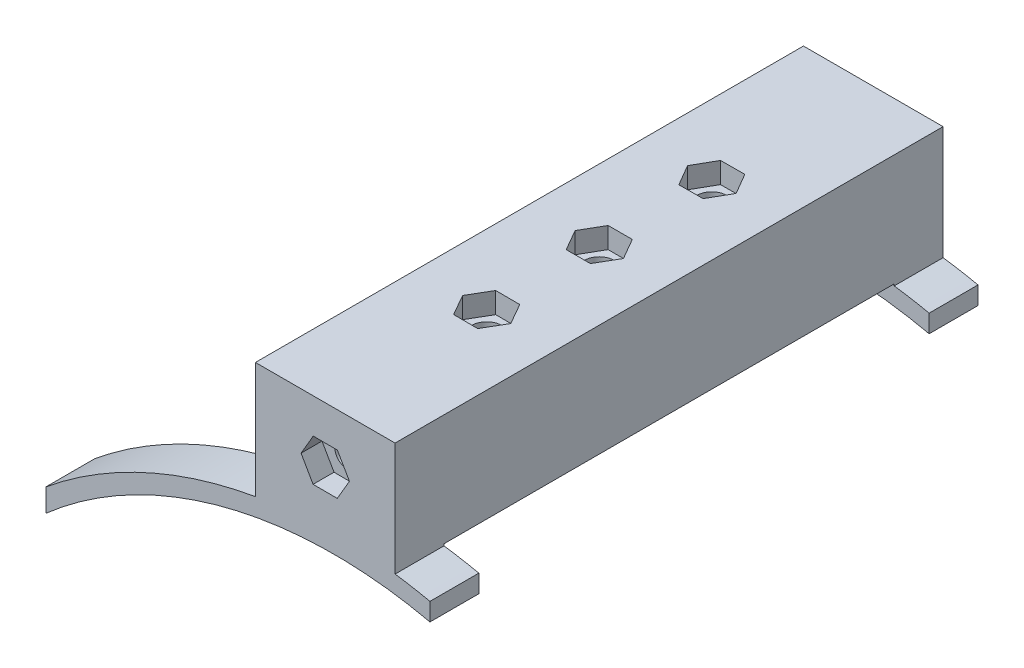
SolidWorks part; units mm, degrees
ref_plane "Front Plane" through (0, 0, 0) normal (0, 0, 1) x (1, 0, 0)
ref_plane "Top Plane" through (0, 0, 0) normal (0, 1, 0) x (1, 0, 0)
ref_plane "Right Plane" through (0, 0, 0) normal (1, 0, 0) x (0, 0, -1)
sketch "Sketch1" plane through (0, 0, 0) normal (0, 0, 1) x (1, 0, 0)
  line L2 (0.4722, 8.3889) -> (0.4722, 5.3889)
  line L3 (0.4722, -7.6111) -> (0.4722, -4.6111)
  line L4 (0.4722, -4.6111) -> (0.4722, 5.3889)
  line L9 (0.4722, 8.3889) -> (-17.5278, 8.3889)
  line L10 (0.4722, 8.3889) -> (0.4722, 5.3889)
  line L12 (0.4722, -7.6111) -> (-17.5278, -7.6111)
  line L13 (-17.5278, 8.3889) -> (-17.5278, -7.6111)
  line L14 (0.4722, 8.3889) -> (-17.5278, -7.6111) construction
  line L15 (0.4722, -7.6111) -> (-17.5278, 8.3889) construction
  line L17 (0.4722, -4.6111) -> (0.4722, -7.6111)
  point P14 (-8.5278, 0.3889)
  dimension "D2" = 18
extrude "Boss-Extrude2" add sketch "Sketch1" along normal blind 48.5
sketch "Sketch2" plane through (-17.5278, 0, 0) normal (-1, 0, 0) x (0, 0, 1)
  line L0 (48.5, 8.3889) -> (62.5, 8.3889)
  line L1 (63.5, 7.3889) -> (63.5, -6.6111)
  line L2 (62.5, -7.6111) -> (48.5, -7.6111)
  line L3 (58.5, -4.6111) -> (58.5, 5.3889) construction
  line L4 (62.5, 8.3889) -> (63.5, 8.3889)
  line L5 (63.5, 8.3889) -> (63.5, 7.3889)
  line L8 (48.5, 8.3889) -> (48.5, -7.6111) construction
  line L12 (48.5, 8.3889) -> (48.5, 5.5889)
  line L13 (48.5, -4.8111) -> (48.5, -7.6111)
  line L14 (24.25, 8.3889) -> (24.25, 19.6589) construction
  line L15 (48.5, 8.3889) -> (0, 8.3889) construction
  line L16 (0, -4.8111) -> (0, -7.6111)
  line L17 (0, 8.3889) -> (0, 5.5889)
  line L21 (-14, -7.6111) -> (0, -7.6111)
  line L22 (-15, 7.3889) -> (-15, -6.6111)
  line L23 (0, 8.3889) -> (-14, 8.3889)
  line L24 (63.5, -6.6111) -> (63.5, -7.6111)
  line L25 (63.5, -7.6111) -> (62.5, -7.6111)
  line L26 (-15, 7.3889) -> (-15, 8.3889)
  line L27 (-15, 8.3889) -> (-14, 8.3889)
  line L28 (-15, -6.6111) -> (-15, -7.6111)
  line L29 (-15, -7.6111) -> (-14, -7.6111)
  line L30 (48.5, 5.5889) -> (48.5, -4.8111)
  line L31 (0, 5.5889) -> (0, -4.8111)
  dimension "D1" = 5
extrude "Boss-Extrude3" add sketch "Sketch2" against normal blind 18
sketch "Sketch3" plane through (0, 0, 63.5) normal (0, 0, 1) x (1, 0, 0)
  circle A0 centre (-9.5278, 0.3889) radius 1.6
  dimension "D1" = 3.2
extrude "Cut-Extrude1" cut sketch "Sketch3" against normal blind 8
ref_plane "Plane1" through (0, 0, 24.25) normal (0, 0, 1) x (1, 0, 0)
mirror "Mirror1" about plane through (0, 0, 24.25) normal (0, 0, 1) of "Cut-Extrude1"
sketch "Sketch4" plane through (0, 0, 63.5) normal (0, 0, 1) x (1, 0, 0)
  line L1 (-7.808, -2.6181) -> (-6.0638, 0.3749)
  line L2 (-6.0638, 0.3749) -> (-7.7837, 3.3819)
  line L3 (-7.7837, 3.3819) -> (-11.2477, 3.3959)
  line L4 (-11.2477, 3.3959) -> (-12.9919, 0.4029)
  line L5 (-12.9919, 0.4029) -> (-11.272, -2.604)
  line L6 (-11.272, -2.604) -> (-7.808, -2.6181)
  circle A0 centre (-9.5278, 0.3889) radius 3 construction
  dimension "D1" = 6
extrude "Cut-Extrude3" cut sketch "Sketch4" against normal blind 3
mirror "Mirror2" about plane through (0, 0, 24.25) normal (0, 0, 1) of "Cut-Extrude3"
sketch "Sketch5" plane through (-17.5278, 0, 0) normal (-1, 0, 0) x (0, 0, 1)
  line L4 (-15, -7.6111) -> (63.5, -7.6111)
  line L5 (63.5, -7.6111) -> (63.5, 8.3889)
  line L6 (63.5, 8.3889) -> (-15, 8.3889)
  line L7 (-15, 8.3889) -> (-15, -7.6111)
  line L8 (-15, -7.6111) -> (63.5, -7.6111)
  line L10 (63.5, 8.3889) -> (-15, 8.3889)
  line L11 (-15, 8.3889) -> (-15, -7.6111)
  line L13 (63.5, -7.6111) -> (63.5, 8.3889)
  dimension "D1" = 0
extrude "Boss-Extrude4" add sketch "Sketch5" along normal blind 2
sketch "Sketch6" plane through (0, 0, 63.5) normal (0, 0, 1) x (1, 0, 0)
  line L2 (-19.5278, -7.6111) -> (-19.5278, -8.2571)
  line L3 (-19.5278, -7.6111) -> (0.4722, -7.6111)
  line L4 (0.4722, -7.6111) -> (0.4722, -7.8678)
  line L5 (-39.5278, -15.2811) -> (-39.5278, -18.1496)
  line L6 (-19.5278, -7.6111) -> (-19.5278, 8.3889) construction
  line L7 (22.9722, -15.2811) -> (22.9722, -18.1496)
  line L8 (-19.5278, -7.6111) -> (-19.5278, 8.3889) construction
  line L9 (0.4722, -7.6111) -> (0.4722, 8.3889) construction
  line L10 (0.4722, -7.6111) -> (-19.5278, -7.6111) construction
  arc A0 (-19.5278, -8.2571) -> (-39.5278, -15.2811) centre (-8.2778, -72.2761) ccw
  arc A1 (22.9722, -18.1496) -> (-39.5278, -18.1496) centre (-8.2778, -72.2761) ccw
  arc A2 (22.9722, -15.2811) -> (0.4722, -7.8678) centre (-8.2778, -72.2761) ccw
  point P22 (-9.5278, -7.6111)
  dimension "D2" = 125
  dimension "D4" = 65
  dimension "D3" = 20
extrude "Boss-Extrude5" add sketch "Sketch6" against normal blind 7
mirror "Mirror3" about plane through (0, 0, 24.25) normal (0, 0, 1) of "Boss-Extrude5"
sketch "Sketch7" plane through (0, 0, 63.5) normal (0, 0, 1) x (1, 0, 0)
  line L0 (22.9722, -18.1496) -> (22.9722, -15.2811) construction
  line L1 (-39.5278, -15.2811) -> (-39.5278, -18.1496) construction
  line L2 (22.9722, -18.1496) -> (22.9722, -15.2811)
  line L3 (-39.5278, -15.2811) -> (-39.5278, -18.1496)
  line L4 (-49.5278, -22.0423) -> (-49.5278, -25.322)
  line L5 (-8.2778, -9.7761) -> (-8.2778, -19.2561) construction
  line L6 (32.9722, -22.0423) -> (32.9722, -25.322)
  arc A0 (32.9722, -25.322) -> (22.9722, -18.1496) centre (-8.2778, -72.2761) ccw
  arc A1 (32.9722, -22.0423) -> (22.9722, -15.2811) centre (-8.2778, -72.2761) ccw
  arc A2 (-19.5278, -8.2571) -> (-39.5278, -15.2811) centre (-8.2778, -72.2761) ccw construction
  arc A3 (22.9722, -18.1496) -> (-39.5278, -18.1496) centre (-8.2778, -72.2761) ccw construction
  arc A4 (-39.5278, -18.1496) -> (-49.5278, -25.322) centre (-8.2778, -72.2761) ccw
  arc A5 (-39.5278, -15.2811) -> (-49.5278, -22.0423) centre (-8.2778, -72.2761) ccw
  dimension "D1" = 10
extrude "Boss-Extrude6" add sketch "Sketch7" against normal blind 7
mirror "Mirror4" about plane through (0, 0, 24.25) normal (0, 0, 1) of "Boss-Extrude6"
sketch "Sketch10" plane through (0, -7.6111, 0) normal (0, -1, 0) x (1, 0, 0)
  line L0 (-9.5278, 56.5) -> (-9.5278, 24.25) construction
  line L1 (0.4722, 56.5) -> (-19.5278, 56.5) construction
  line L2 (-9.5278, 24.25) -> (-9.5278, -8) construction
  line L3 (32.9722, -8) -> (-49.5278, -8) construction
  circle A0 centre (-9.5278, 40.375) radius 2.1
  circle A1 centre (-9.5278, 8.125) radius 2.1
  circle A2 centre (-9.5278, 24.25) radius 2.1
  dimension "D1" = 4.2
  dimension "D2" = 4.2
extrude "Cut-Extrude4" cut sketch "Sketch10" against normal through all
sketch "Sketch11" plane through (0, 8.3889, 0) normal (0, 1, 0) x (1, 0, 0)
  line L0 (-9.5278, -24.25) -> (0, -24.25) construction
  line L1 (-7.7805, -11.1161) -> (-6.0638, -8.1073)
  line L2 (-6.0638, -8.1073) -> (-7.8111, -5.1162)
  line L3 (-7.8111, -5.1162) -> (-11.2752, -5.1339)
  line L4 (-11.2752, -5.1339) -> (-12.9919, -8.1427)
  line L5 (-12.9919, -8.1427) -> (-11.2446, -11.1338)
  line L6 (-11.2446, -11.1338) -> (-7.7805, -11.1161)
  line L7 (-18.541, -24.25) -> (18.541, -24.25) construction
  line L8 (-11.2446, -37.3662) -> (-7.7805, -37.3839)
  line L9 (-12.9919, -40.3573) -> (-11.2446, -37.3662)
  line L10 (-11.2752, -43.3661) -> (-12.9919, -40.3573)
  line L11 (-7.8111, -43.3838) -> (-11.2752, -43.3661)
  line L12 (-6.0638, -40.3927) -> (-7.8111, -43.3838)
  line L13 (-7.7805, -37.3839) -> (-6.0638, -40.3927)
  line L15 (-6.0637, -24.25) -> (-7.7958, -21.25)
  line L16 (-7.7958, -21.25) -> (-11.2599, -21.25)
  line L17 (-11.2599, -21.25) -> (-12.992, -24.25)
  line L18 (-12.992, -24.25) -> (-11.2599, -27.25)
  line L19 (-11.2599, -27.25) -> (-7.7958, -27.25)
  line L20 (-7.7958, -27.25) -> (-6.0637, -24.25)
  circle A0 centre (-9.5278, -8.125) radius 3 construction
  circle A1 centre (-9.5278, -40.375) radius 3 construction
  circle A2 centre (-9.5278, -24.25) radius 3 construction
  dimension "D1" = 6
  dimension "D2" = 6
extrude "Cut-Extrude5" cut sketch "Sketch11" against normal blind 3
sketch "Sketch12" plane through (0, 0, 63.5) normal (0, 0, 1) x (1, 0, 0)
  line L0 (5.4722, -8.7471) -> (5.4722, -11.3074)
  line L1 (5.4722, -8.7471) -> (5.4722, -11.3074) construction
  line L7 (0.4722, 8.3889) -> (-19.5278, 8.3889)
  line L8 (-19.5278, 8.3889) -> (-19.5278, -8.2571)
  line L9 (-49.5278, -22.0423) -> (-49.5278, -25.322)
  line L10 (32.9722, -25.322) -> (32.9722, -22.0423)
  line L11 (0.4722, -7.8678) -> (0.4722, 8.3889)
  line L15 (32.9722, -25.322) -> (32.9722, -22.0423)
  arc A0 (32.9722, -22.0423) -> (0.4722, -7.8678) centre (-8.2778, -72.2761) ccw construction
  arc A1 (32.9722, -25.322) -> (-49.5278, -25.322) centre (-8.2778, -72.2761) ccw construction
  arc A5 (-19.5278, -8.2571) -> (-49.5278, -22.0423) centre (-8.2778, -72.2761) ccw
  arc A6 (32.9722, -25.322) -> (-49.5278, -25.322) centre (-8.2778, -72.2761) ccw
  arc A7 (32.9722, -22.0423) -> (0.4722, -7.8678) centre (-8.2778, -72.2761) ccw
  arc A9 (32.9722, -25.322) -> (5.4722, -11.3074) centre (-8.2778, -72.2761) ccw
  arc A10 (32.9722, -22.0423) -> (5.4722, -8.7471) centre (-8.2778, -72.2761) ccw
  dimension "D1" = 0
extrude "Cut-Extrude6" cut sketch "Sketch12" against normal through all
